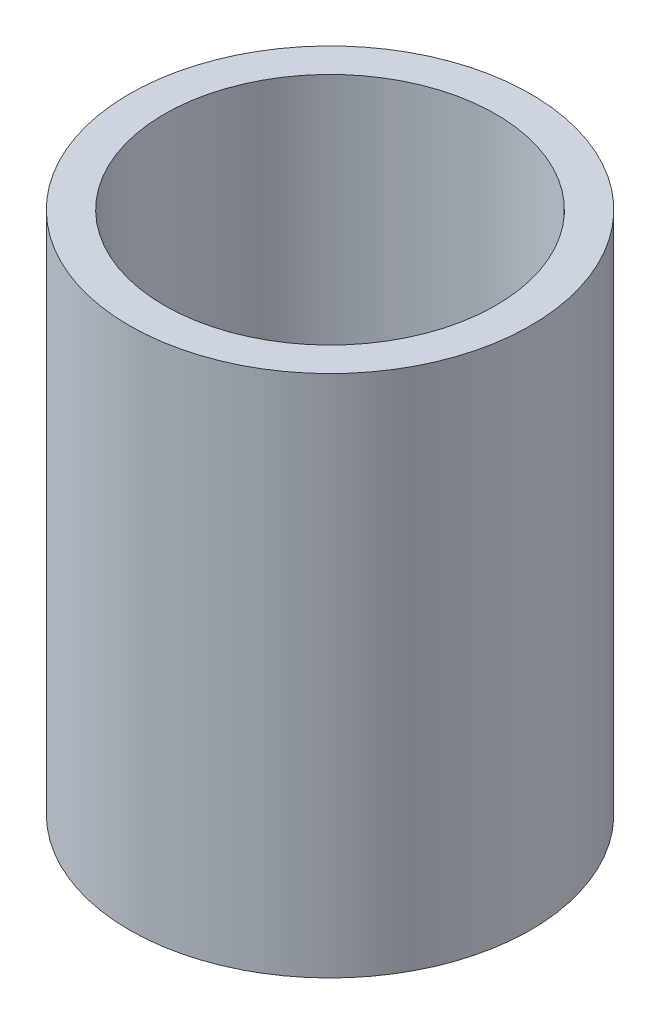
SolidWorks part; units mm, degrees
ref_plane "Front Plane" through (0, 0, 0) normal (0, 0, 1) x (1, 0, 0)
ref_plane "Top Plane" through (0, 0, 0) normal (0, 1, 0) x (1, 0, 0)
ref_plane "Right Plane" through (0, 0, 0) normal (1, 0, 0) x (0, 0, -1)
sketch "Sketch1" plane through (0, 0, 0) normal (0, 1, 0) x (1, 0, 0)
  circle A0 centre (-0.9295, 1.2067) radius 1.9
  circle A1 centre (-0.9295, 1.2067) radius 2.3
  dimension "D1" = 3.8
  dimension "D2" = 4.6
extrude "Boss-Extrude1" add sketch "Sketch1" along normal blind 6
